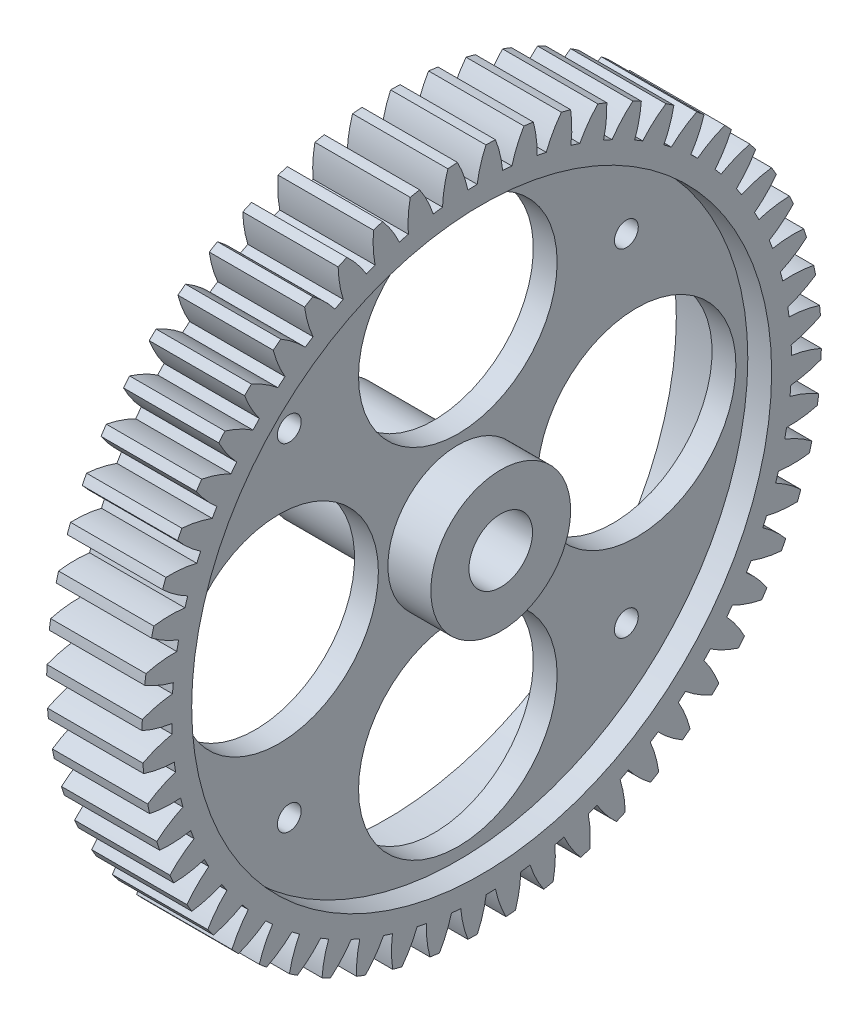
SolidWorks part; units mm, degrees
ref_plane "Front Plane" through (0, 0, 0) normal (0, 0, 1) x (1, 0, 0)
ref_plane "Top Plane" through (0, 0, 0) normal (0, 1, 0) x (1, 0, 0)
ref_plane "Right Plane" through (0, 0, 0) normal (1, 0, 0) x (0, 0, -1)
sketch "Sketch1" plane through (0, 0, 0) normal (1, 0, 0) x (0, 0, -1)
  line L0 (0, 0) -> (0.1063, 3.9986) construction
  line L1 (1.0369, 38.9862) -> (1.1366, 42.7349) construction
  line L2 (22.5, 0) -> (0, 0) construction
  line L3 (0, 0) -> (21.2132, -21.2132) construction
  circle A0 centre (0, 0) radius 42.75 construction
  circle A1 centre (0, 0) radius 41.375 construction
  circle A2 centre (0, 0) radius 39 construction
  circle A3 centre (0, 0) radius 4
  arc A4 (0, 41.375) -> (2.1992, 41.3165) centre (0, 0) cw
  arc A5 (-0.5634, 38.9959) -> (2.6354, 38.9109) centre (0, 0) cw
  arc A6 (0.5367, 42.7466) -> (1.7362, 42.7147) centre (0, 0) cw
  arc A7 (1.7362, 42.7147) -> (2.6354, 38.9109) centre (-11.2723, 37.6315) cw
  arc A8 (0.5367, 42.7466) -> (-0.5634, 38.9959) centre (13.2566, 36.9791) ccw
  arc A9 (5.3194, 42.4178) -> (3.8063, 38.8138) centre (17.3136, 35.2623) ccw
  arc A10 (3.8063, 38.8138) -> (6.9755, 38.3711) centre (0, 0) cw
  arc A11 (6.5078, 42.2518) -> (6.9755, 38.3711) centre (-6.988, 38.6569) cw
  arc A12 (5.3194, 42.4178) -> (6.5078, 42.2518) centre (0, 0) cw
  arc A13 (10.0352, 41.5555) -> (8.1281, 38.1436) centre (21.1529, 33.1021) ccw
  arc A14 (8.1281, 38.1436) -> (11.2278, 37.3488) centre (0, 0) cw
  arc A15 (11.1976, 41.2574) -> (11.2278, 37.3488) centre (-2.6159, 39.1963) cw
  arc A16 (10.0352, 41.5555) -> (11.1976, 41.2574) centre (0, 0) cw
  arc A17 (14.6249, 40.1706) -> (12.3477, 36.9937) centre (24.7261, 30.5256) ccw
  arc A18 (12.3477, 36.9937) -> (15.339, 35.8569) centre (0, 0) cw
  arc A19 (15.7466, 39.7443) -> (15.339, 35.8569) centre (1.7891, 39.2427) cw
  arc A20 (14.6249, 40.1706) -> (15.7466, 39.7443) centre (0, 0) cw
  arc A21 (19.0306, 38.2805) -> (16.412, 35.3786) centre (27.9884, 27.5652) ccw
  arc A22 (16.412, 35.3786) -> (19.2572, 33.914) centre (0, 0) cw
  arc A23 (20.0975, 37.7313) -> (19.2572, 33.914) centre (6.1717, 38.7956) cw
  arc A24 (19.0306, 38.2805) -> (20.0975, 37.7313) centre (0, 0) cw
  arc A25 (23.197, 35.9091) -> (20.27, 33.3186) centre (30.8988, 24.2582) ccw
  arc A26 (20.27, 33.3186) -> (22.9333, 31.5446) centre (0, 0) cw
  arc A27 (24.1957, 35.2439) -> (22.9333, 31.5446) centre (10.4766, 37.8607) cw
  arc A28 (23.197, 35.9091) -> (24.1957, 35.2439) centre (0, 0) cw
  arc A29 (27.0717, 33.0861) -> (23.873, 30.8396) centre (33.4205, 20.6461) ccw
  arc A30 (23.873, 30.8396) -> (26.321, 28.7786) centre (0, 0) cw
  arc A31 (27.9896, 32.3132) -> (26.321, 28.7786) centre (14.6498, 36.4496) cw
  arc A32 (27.0717, 33.0861) -> (27.9896, 32.3132) centre (0, 0) cw
  arc A33 (30.6059, 29.847) -> (27.1759, 27.9727) centre (35.522, 16.7743) ccw
  arc A34 (27.1759, 27.9727) -> (29.3777, 25.6506) centre (0, 0) cw
  arc A35 (31.4316, 28.9762) -> (29.3777, 25.6506) centre (18.6387, 34.5802) cw
  arc A36 (30.6059, 29.847) -> (31.4316, 28.9762) centre (0, 0) cw
  arc A37 (33.7553, 26.2325) -> (30.1369, 24.7541) centre (37.1768, 12.6917) ccw
  arc A38 (30.1369, 24.7541) -> (32.0649, 22.2001) centre (0, 0) cw
  arc A39 (34.4782, 25.2748) -> (32.0649, 22.2001) centre (22.3933, 32.2759) cw
  arc A40 (33.7553, 26.2325) -> (34.4782, 25.2748) centre (0, 0) cw
  arc A41 (36.4801, 22.2882) -> (32.719, 21.2242) centre (38.364, 8.4494) ccw
  arc A42 (32.719, 21.2242) -> (34.3489, 18.4703) centre (0, 0) cw
  arc A43 (37.0913, 21.2555) -> (34.3489, 18.4703) centre (25.8662, 29.5657) cw
  arc A44 (36.4801, 22.2882) -> (37.0913, 21.2555) centre (0, 0) cw
  arc A45 (38.7462, 18.0636) -> (34.8896, 17.4274) centre (39.0688, 4.1008) ccw
  arc A46 (34.8896, 17.4274) -> (36.2009, 14.5084) centre (0, 0) cw
  arc A47 (39.238, 16.9689) -> (36.2009, 14.5084) centre (29.0139, 26.4837) cw
  arc A48 (38.7462, 18.0636) -> (39.238, 16.9689) centre (0, 0) cw
  arc A49 (40.5251, 13.6118) -> (36.6215, 13.4114) centre (39.2823, -0.2993) ccw
  arc A50 (36.6215, 13.4114) -> (37.5977, 10.3639) centre (0, 0) cw
  arc A51 (40.8912, 12.469) -> (37.5977, 10.3639) centre (31.7967, 23.0686) cw
  arc A52 (40.5251, 13.6118) -> (40.8912, 12.469) centre (0, 0) cw
  arc A53 (41.7943, 8.9888) -> (37.8928, 9.2267) centre (39.0018, -4.6956) ccw
  arc A54 (37.8928, 9.2267) -> (38.5217, 6.0891) centre (0, 0) cw
  arc A55 (42.0301, 7.8122) -> (38.5217, 6.0891) centre (34.1796, 19.3635) cw
  arc A56 (41.7943, 8.9888) -> (42.0301, 7.8122) centre (0, 0) cw
  arc A57 (42.5379, 4.2528) -> (38.6876, 4.9261) centre (38.2309, -9.0329) ccw
  arc A58 (38.6876, 4.9261) -> (38.9613, 1.7378) centre (0, 0) cw
  arc A59 (42.6405, 3.0572) -> (38.9613, 1.7378) centre (36.1327, 15.4148) cw
  arc A60 (42.5379, 4.2528) -> (42.6405, 3.0572) centre (0, 0) cw
  arc A61 (42.7466, -0.5367) -> (38.9959, 0.5634) centre (36.9791, -13.2566) ccw
  arc A62 (38.9959, 0.5634) -> (38.9109, -2.6354) centre (0, 0) cw
  arc A63 (42.7147, -1.7362) -> (38.9109, -2.6354) centre (37.6315, 11.2723) cw
  arc A64 (42.7466, -0.5367) -> (42.7147, -1.7362) centre (0, 0) cw
  arc A65 (42.4178, -5.3194) -> (38.8138, -3.8063) centre (35.2623, -17.3136) ccw
  arc A66 (38.8138, -3.8063) -> (38.3711, -6.9755) centre (0, 0) cw
  arc A67 (42.2518, -6.5078) -> (38.3711, -6.9755) centre (38.6569, 6.988) cw
  arc A68 (42.4178, -5.3194) -> (42.2518, -6.5078) centre (0, 0) cw
  arc A69 (41.5555, -10.0352) -> (38.1436, -8.1281) centre (33.1021, -21.1529) ccw
  arc A70 (38.1436, -8.1281) -> (37.3488, -11.2278) centre (0, 0) cw
  arc A71 (41.2574, -11.1976) -> (37.3488, -11.2278) centre (39.1963, 2.6159) cw
  arc A72 (41.5555, -10.0352) -> (41.2574, -11.1976) centre (0, 0) cw
  arc A73 (40.1706, -14.6249) -> (36.9937, -12.3477) centre (30.5256, -24.7261) ccw
  arc A74 (36.9937, -12.3477) -> (35.8569, -15.339) centre (0, 0) cw
  arc A75 (39.7443, -15.7466) -> (35.8569, -15.339) centre (39.2427, -1.7891) cw
  arc A76 (40.1706, -14.6249) -> (39.7443, -15.7466) centre (0, 0) cw
  arc A77 (38.2805, -19.0306) -> (35.3786, -16.412) centre (27.5652, -27.9884) ccw
  arc A78 (35.3786, -16.412) -> (33.914, -19.2572) centre (0, 0) cw
  arc A79 (37.7313, -20.0975) -> (33.914, -19.2572) centre (38.7956, -6.1717) cw
  arc A80 (38.2805, -19.0306) -> (37.7313, -20.0975) centre (0, 0) cw
  arc A81 (35.9091, -23.197) -> (33.3186, -20.27) centre (24.2582, -30.8988) ccw
  arc A82 (33.3186, -20.27) -> (31.5446, -22.9333) centre (0, 0) cw
  arc A83 (35.2439, -24.1957) -> (31.5446, -22.9333) centre (37.8607, -10.4766) cw
  arc A84 (35.9091, -23.197) -> (35.2439, -24.1957) centre (0, 0) cw
  arc A85 (33.0861, -27.0717) -> (30.8396, -23.873) centre (20.6461, -33.4205) ccw
  arc A86 (30.8396, -23.873) -> (28.7786, -26.321) centre (0, 0) cw
  arc A87 (32.3132, -27.9896) -> (28.7786, -26.321) centre (36.4496, -14.6498) cw
  arc A88 (33.0861, -27.0717) -> (32.3132, -27.9896) centre (0, 0) cw
  arc A89 (29.847, -30.6059) -> (27.9727, -27.1759) centre (16.7743, -35.522) ccw
  arc A90 (27.9727, -27.1759) -> (25.6506, -29.3777) centre (0, 0) cw
  arc A91 (28.9762, -31.4316) -> (25.6506, -29.3777) centre (34.5802, -18.6387) cw
  arc A92 (29.847, -30.6059) -> (28.9762, -31.4316) centre (0, 0) cw
  arc A93 (26.2325, -33.7553) -> (24.7541, -30.1369) centre (12.6917, -37.1768) ccw
  arc A94 (24.7541, -30.1369) -> (22.2001, -32.0649) centre (0, 0) cw
  arc A95 (25.2748, -34.4782) -> (22.2001, -32.0649) centre (32.2759, -22.3933) cw
  arc A96 (26.2325, -33.7553) -> (25.2748, -34.4782) centre (0, 0) cw
  arc A97 (22.2882, -36.4801) -> (21.2242, -32.719) centre (8.4494, -38.364) ccw
  arc A98 (21.2242, -32.719) -> (18.4703, -34.3489) centre (0, 0) cw
  arc A99 (21.2555, -37.0913) -> (18.4703, -34.3489) centre (29.5657, -25.8662) cw
  arc A100 (22.2882, -36.4801) -> (21.2555, -37.0913) centre (0, 0) cw
  arc A101 (18.0636, -38.7462) -> (17.4274, -34.8896) centre (4.1008, -39.0688) ccw
  arc A102 (17.4274, -34.8896) -> (14.5084, -36.2009) centre (0, 0) cw
  arc A103 (16.9689, -39.238) -> (14.5084, -36.2009) centre (26.4837, -29.0139) cw
  arc A104 (18.0636, -38.7462) -> (16.9689, -39.238) centre (0, 0) cw
  arc A105 (13.6118, -40.5251) -> (13.4114, -36.6215) centre (-0.2993, -39.2823) ccw
  arc A106 (13.4114, -36.6215) -> (10.3639, -37.5977) centre (0, 0) cw
  arc A107 (12.469, -40.8912) -> (10.3639, -37.5977) centre (23.0686, -31.7967) cw
  arc A108 (13.6118, -40.5251) -> (12.469, -40.8912) centre (0, 0) cw
  arc A109 (8.9888, -41.7943) -> (9.2267, -37.8928) centre (-4.6956, -39.0018) ccw
  arc A110 (9.2267, -37.8928) -> (6.0891, -38.5217) centre (0, 0) cw
  arc A111 (7.8122, -42.0301) -> (6.0891, -38.5217) centre (19.3635, -34.1796) cw
  arc A112 (8.9888, -41.7943) -> (7.8122, -42.0301) centre (0, 0) cw
  arc A113 (4.2528, -42.5379) -> (4.9261, -38.6876) centre (-9.0329, -38.2309) ccw
  arc A114 (4.9261, -38.6876) -> (1.7378, -38.9613) centre (0, 0) cw
  arc A115 (3.0572, -42.6405) -> (1.7378, -38.9613) centre (15.4148, -36.1327) cw
  arc A116 (4.2528, -42.5379) -> (3.0572, -42.6405) centre (0, 0) cw
  arc A117 (-0.5367, -42.7466) -> (0.5634, -38.9959) centre (-13.2566, -36.9791) ccw
  arc A118 (0.5634, -38.9959) -> (-2.6354, -38.9109) centre (0, 0) cw
  arc A119 (-1.7362, -42.7147) -> (-2.6354, -38.9109) centre (11.2723, -37.6315) cw
  arc A120 (-0.5367, -42.7466) -> (-1.7362, -42.7147) centre (0, 0) cw
  arc A121 (-5.3194, -42.4178) -> (-3.8063, -38.8138) centre (-17.3136, -35.2623) ccw
  arc A122 (-3.8063, -38.8138) -> (-6.9755, -38.3711) centre (0, 0) cw
  arc A123 (-6.5078, -42.2518) -> (-6.9755, -38.3711) centre (6.988, -38.6569) cw
  arc A124 (-5.3194, -42.4178) -> (-6.5078, -42.2518) centre (0, 0) cw
  arc A125 (-10.0352, -41.5555) -> (-8.1281, -38.1436) centre (-21.1529, -33.1021) ccw
  arc A126 (-8.1281, -38.1436) -> (-11.2278, -37.3488) centre (0, 0) cw
  arc A127 (-11.1976, -41.2574) -> (-11.2278, -37.3488) centre (2.6159, -39.1963) cw
  arc A128 (-10.0352, -41.5555) -> (-11.1976, -41.2574) centre (0, 0) cw
  arc A129 (-14.6249, -40.1706) -> (-12.3477, -36.9937) centre (-24.7261, -30.5256) ccw
  arc A130 (-12.3477, -36.9937) -> (-15.339, -35.8569) centre (0, 0) cw
  arc A131 (-15.7466, -39.7443) -> (-15.339, -35.8569) centre (-1.7891, -39.2427) cw
  arc A132 (-14.6249, -40.1706) -> (-15.7466, -39.7443) centre (0, 0) cw
  arc A133 (-19.0306, -38.2805) -> (-16.412, -35.3786) centre (-27.9884, -27.5652) ccw
  arc A134 (-16.412, -35.3786) -> (-19.2572, -33.914) centre (0, 0) cw
  arc A135 (-20.0975, -37.7313) -> (-19.2572, -33.914) centre (-6.1717, -38.7956) cw
  arc A136 (-19.0306, -38.2805) -> (-20.0975, -37.7313) centre (0, 0) cw
  arc A137 (-23.197, -35.9091) -> (-20.27, -33.3186) centre (-30.8988, -24.2582) ccw
  arc A138 (-20.27, -33.3186) -> (-22.9333, -31.5446) centre (0, 0) cw
  arc A139 (-24.1957, -35.2439) -> (-22.9333, -31.5446) centre (-10.4766, -37.8607) cw
  arc A140 (-23.197, -35.9091) -> (-24.1957, -35.2439) centre (0, 0) cw
  arc A141 (-27.0717, -33.0861) -> (-23.873, -30.8396) centre (-33.4205, -20.6461) ccw
  arc A142 (-23.873, -30.8396) -> (-26.321, -28.7786) centre (0, 0) cw
  arc A143 (-27.9896, -32.3132) -> (-26.321, -28.7786) centre (-14.6498, -36.4496) cw
  arc A144 (-27.0717, -33.0861) -> (-27.9896, -32.3132) centre (0, 0) cw
  arc A145 (-30.6059, -29.847) -> (-27.1759, -27.9727) centre (-35.522, -16.7743) ccw
  arc A146 (-27.1759, -27.9727) -> (-29.3777, -25.6506) centre (0, 0) cw
  arc A147 (-31.4316, -28.9762) -> (-29.3777, -25.6506) centre (-18.6387, -34.5802) cw
  arc A148 (-30.6059, -29.847) -> (-31.4316, -28.9762) centre (0, 0) cw
  arc A149 (-33.7553, -26.2325) -> (-30.1369, -24.7541) centre (-37.1768, -12.6917) ccw
  arc A150 (-30.1369, -24.7541) -> (-32.0649, -22.2001) centre (0, 0) cw
  arc A151 (-34.4782, -25.2748) -> (-32.0649, -22.2001) centre (-22.3933, -32.2759) cw
  arc A152 (-33.7553, -26.2325) -> (-34.4782, -25.2748) centre (0, 0) cw
  arc A153 (-36.4801, -22.2882) -> (-32.719, -21.2242) centre (-38.364, -8.4494) ccw
  arc A154 (-32.719, -21.2242) -> (-34.3489, -18.4703) centre (0, 0) cw
  arc A155 (-37.0913, -21.2555) -> (-34.3489, -18.4703) centre (-25.8662, -29.5657) cw
  arc A156 (-36.4801, -22.2882) -> (-37.0913, -21.2555) centre (0, 0) cw
  arc A157 (-38.7462, -18.0636) -> (-34.8896, -17.4274) centre (-39.0688, -4.1008) ccw
  arc A158 (-34.8896, -17.4274) -> (-36.2009, -14.5084) centre (0, 0) cw
  arc A159 (-39.238, -16.9689) -> (-36.2009, -14.5084) centre (-29.0139, -26.4837) cw
  arc A160 (-38.7462, -18.0636) -> (-39.238, -16.9689) centre (0, 0) cw
  arc A161 (-40.5251, -13.6118) -> (-36.6215, -13.4114) centre (-39.2823, 0.2993) ccw
  arc A162 (-36.6215, -13.4114) -> (-37.5977, -10.3639) centre (0, 0) cw
  arc A163 (-40.8912, -12.469) -> (-37.5977, -10.3639) centre (-31.7967, -23.0686) cw
  arc A164 (-40.5251, -13.6118) -> (-40.8912, -12.469) centre (0, 0) cw
  arc A165 (-41.7943, -8.9888) -> (-37.8928, -9.2267) centre (-39.0018, 4.6956) ccw
  arc A166 (-37.8928, -9.2267) -> (-38.5217, -6.0891) centre (0, 0) cw
  arc A167 (-42.0301, -7.8122) -> (-38.5217, -6.0891) centre (-34.1796, -19.3635) cw
  arc A168 (-41.7943, -8.9888) -> (-42.0301, -7.8122) centre (0, 0) cw
  arc A169 (-42.5379, -4.2528) -> (-38.6876, -4.9261) centre (-38.2309, 9.0329) ccw
  arc A170 (-38.6876, -4.9261) -> (-38.9613, -1.7378) centre (0, 0) cw
  arc A171 (-42.6405, -3.0572) -> (-38.9613, -1.7378) centre (-36.1327, -15.4148) cw
  arc A172 (-42.5379, -4.2528) -> (-42.6405, -3.0572) centre (0, 0) cw
  arc A173 (-42.7466, 0.5367) -> (-38.9959, -0.5634) centre (-36.9791, 13.2566) ccw
  arc A174 (-38.9959, -0.5634) -> (-38.9109, 2.6354) centre (0, 0) cw
  arc A175 (-42.7147, 1.7362) -> (-38.9109, 2.6354) centre (-37.6315, -11.2723) cw
  arc A176 (-42.7466, 0.5367) -> (-42.7147, 1.7362) centre (0, 0) cw
  arc A177 (-42.4178, 5.3194) -> (-38.8138, 3.8063) centre (-35.2623, 17.3136) ccw
  arc A178 (-38.8138, 3.8063) -> (-38.3711, 6.9755) centre (0, 0) cw
  arc A179 (-42.2518, 6.5078) -> (-38.3711, 6.9755) centre (-38.6569, -6.988) cw
  arc A180 (-42.4178, 5.3194) -> (-42.2518, 6.5078) centre (0, 0) cw
  arc A181 (-41.5555, 10.0352) -> (-38.1436, 8.1281) centre (-33.1021, 21.1529) ccw
  arc A182 (-38.1436, 8.1281) -> (-37.3488, 11.2278) centre (0, 0) cw
  arc A183 (-41.2574, 11.1976) -> (-37.3488, 11.2278) centre (-39.1963, -2.6159) cw
  arc A184 (-41.5555, 10.0352) -> (-41.2574, 11.1976) centre (0, 0) cw
  arc A185 (-40.1706, 14.6249) -> (-36.9937, 12.3477) centre (-30.5256, 24.7261) ccw
  arc A186 (-36.9937, 12.3477) -> (-35.8569, 15.339) centre (0, 0) cw
  arc A187 (-39.7443, 15.7466) -> (-35.8569, 15.339) centre (-39.2427, 1.7891) cw
  arc A188 (-40.1706, 14.6249) -> (-39.7443, 15.7466) centre (0, 0) cw
  arc A189 (-38.2805, 19.0306) -> (-35.3786, 16.412) centre (-27.5652, 27.9884) ccw
  arc A190 (-35.3786, 16.412) -> (-33.914, 19.2572) centre (0, 0) cw
  arc A191 (-37.7313, 20.0975) -> (-33.914, 19.2572) centre (-38.7956, 6.1717) cw
  arc A192 (-38.2805, 19.0306) -> (-37.7313, 20.0975) centre (0, 0) cw
  arc A193 (-35.9091, 23.197) -> (-33.3186, 20.27) centre (-24.2582, 30.8988) ccw
  arc A194 (-33.3186, 20.27) -> (-31.5446, 22.9333) centre (0, 0) cw
  arc A195 (-35.2439, 24.1957) -> (-31.5446, 22.9333) centre (-37.8607, 10.4766) cw
  arc A196 (-35.9091, 23.197) -> (-35.2439, 24.1957) centre (0, 0) cw
  arc A197 (-33.0861, 27.0717) -> (-30.8396, 23.873) centre (-20.6461, 33.4205) ccw
  arc A198 (-30.8396, 23.873) -> (-28.7786, 26.321) centre (0, 0) cw
  arc A199 (-32.3132, 27.9896) -> (-28.7786, 26.321) centre (-36.4496, 14.6498) cw
  arc A200 (-33.0861, 27.0717) -> (-32.3132, 27.9896) centre (0, 0) cw
  arc A201 (-29.847, 30.6059) -> (-27.9727, 27.1759) centre (-16.7743, 35.522) ccw
  arc A202 (-27.9727, 27.1759) -> (-25.6506, 29.3777) centre (0, 0) cw
  arc A203 (-28.9762, 31.4316) -> (-25.6506, 29.3777) centre (-34.5802, 18.6387) cw
  arc A204 (-29.847, 30.6059) -> (-28.9762, 31.4316) centre (0, 0) cw
  arc A205 (-26.2325, 33.7553) -> (-24.7541, 30.1369) centre (-12.6917, 37.1768) ccw
  arc A206 (-24.7541, 30.1369) -> (-22.2001, 32.0649) centre (0, 0) cw
  arc A207 (-25.2748, 34.4782) -> (-22.2001, 32.0649) centre (-32.2759, 22.3933) cw
  arc A208 (-26.2325, 33.7553) -> (-25.2748, 34.4782) centre (0, 0) cw
  arc A209 (-22.2882, 36.4801) -> (-21.2242, 32.719) centre (-8.4494, 38.364) ccw
  arc A210 (-21.2242, 32.719) -> (-18.4703, 34.3489) centre (0, 0) cw
  arc A211 (-21.2555, 37.0913) -> (-18.4703, 34.3489) centre (-29.5657, 25.8662) cw
  arc A212 (-22.2882, 36.4801) -> (-21.2555, 37.0913) centre (0, 0) cw
  arc A213 (-18.0636, 38.7462) -> (-17.4274, 34.8896) centre (-4.1008, 39.0688) ccw
  arc A214 (-17.4274, 34.8896) -> (-14.5084, 36.2009) centre (0, 0) cw
  arc A215 (-16.9689, 39.238) -> (-14.5084, 36.2009) centre (-26.4837, 29.0139) cw
  arc A216 (-18.0636, 38.7462) -> (-16.9689, 39.238) centre (0, 0) cw
  arc A217 (-13.6118, 40.5251) -> (-13.4114, 36.6215) centre (0.2993, 39.2823) ccw
  arc A218 (-13.4114, 36.6215) -> (-10.3639, 37.5977) centre (0, 0) cw
  arc A219 (-12.469, 40.8912) -> (-10.3639, 37.5977) centre (-23.0686, 31.7967) cw
  arc A220 (-13.6118, 40.5251) -> (-12.469, 40.8912) centre (0, 0) cw
  arc A221 (-8.9888, 41.7943) -> (-9.2267, 37.8928) centre (4.6956, 39.0018) ccw
  arc A222 (-9.2267, 37.8928) -> (-6.0891, 38.5217) centre (0, 0) cw
  arc A223 (-7.8122, 42.0301) -> (-6.0891, 38.5217) centre (-19.3635, 34.1796) cw
  arc A224 (-8.9888, 41.7943) -> (-7.8122, 42.0301) centre (0, 0) cw
  arc A225 (-4.2528, 42.5379) -> (-4.9261, 38.6876) centre (9.0329, 38.2309) ccw
  arc A226 (-4.9261, 38.6876) -> (-1.7378, 38.9613) centre (0, 0) cw
  arc A227 (-3.0572, 42.6405) -> (-1.7378, 38.9613) centre (-15.4148, 36.1327) cw
  arc A228 (-4.2528, 42.5379) -> (-3.0572, 42.6405) centre (0, 0) cw
  circle A229 centre (0, 0) radius 39
  circle A230 centre (0, 0) radius 22.5 construction
  circle A231 centre (0, 22.5) radius 12.5
  circle A234 centre (22.5, 0) radius 12.5
  circle A235 centre (0, -22.5) radius 12.5
  circle A236 centre (-22.5, 0) radius 12.5
  circle A237 centre (0, 0) radius 30 construction
  circle A238 centre (21.2132, -21.2132) radius 1.5
  circle A239 centre (-21.2132, -21.2132) radius 1.5
  circle A240 centre (-21.2132, 21.2132) radius 1.5
  circle A241 centre (21.2132, 21.2132) radius 1.5
  point P13 (1.0369, 38.9862)
  point P16 (1.1366, 42.7349)
  point P351 (0, 0)
  point P360 (0, 0)
  point P364 (0, 0)
  point P374 (0, 0)
  dimension "D1" = 85.5
  dimension "D2" = 82.75
  dimension "D3" = 78
  dimension "D4" = 8
  dimension "D5" = 2.2
  dimension "D9" = 45
  dimension "D10" = 4
  dimension "D6" = 3.2
  dimension "D7" = 1.2
  dimension "D8" = 56
extrude "Boss-Extrude1" add sketch "Sketch1" along normal blind 12 contours A62 A229 A58 A54 A50 A46 A42 A38 A34 A30 A26 A22 A18 A14 A10 A5 A226 A222 A218 A214 A210 A206 A202 A198 A194 A190 A186 | A144 A141 A142 A143 | A140 A137 A138 A139 | A136 A133 A134 A135 | A132 A129 A130 A131 | A128 A125 A126 A127 | A124 A121 A122 A123 | A120 A117 A118 A119 | A116 A113 A114 A115 | A112 A109 A110 A111 | A108 A105 A106 A107 | A104 A101 A102 A103 | A100 A97 A98 A99 | A96 A93 A94 A95 | A92 A89 A90 A91 | A88 A85 A86 A87 | A84 A81 A82 A83 | A148 A145 A146 A147 | A152 A149 A150 A151 | A156 A153 A154 A155 | A160 A157 A158 A159 | A164 A161 A162 A163 | A168 A165 A166 A167 | A172 A169 A170 A171 | A176 A173 A174 A175 | A180 A177 A178 A179 | A184 A181 A182 A183 | A60 A57 A58 A59 | A64 A61 A62 A63 | A68 A65 A66 A67 | A72 A69 A70 A71 | A76 A73 A74 A75 | A80 A77 A78 A79 | A188 A185 A186 A187 | A192 A189 A190 A191 | A196 A193 A194 A195 | A200 A197 A198 A199 | A204 A201 A202 A203 | A208 A205 A206 A207 | A212 A209 A210 A211 | A216 A213 A214 A215 | A220 A217 A218 A219 | A224 A221 A222 A223 | A228 A225 A226 A227 | A12 A9 A10 A11 | A16 A13 A14 A15 | A20 A17 A18 A19 | A56 A53 A54 A55 | A52 A49 A50 A51 | A48 A45 A46 A47 | A44 A41 A42 A43 | A40 A37 A38 A39 | A36 A33 A34 A35 | A32 A29 A30 A31 | A28 A25 A26 A27 | A24 A21 A22 A23 | A6 A8 A4 A7 | A4 A8 A5 A7
sketch "Sketch4" plane through (12, 0, 0) normal (1, 0, 0) x (0, 0, -1)
  circle A0 centre (0, 0) radius 36.5
extrude "Cut-Extrude1" cut sketch "Sketch4" against normal blind 3
sketch "Sketch5" plane through (0, 0, 0) normal (-1, 0, 0) x (0, 0, 1)
  circle A0 centre (0, 0) radius 36.5
extrude "Cut-Extrude2" cut sketch "Sketch5" against normal blind 6
sketch "Sketch6" plane through (9, 0, 0) normal (1, 0, 0) x (0, 0, -1)
  circle A0 centre (0, 0) radius 8.8
  circle A1 centre (0, 0) radius 4
  dimension "D1" = 17.6
extrude "Boss-Extrude2" add sketch "Sketch6" along normal blind 5.4
sketch "Sketch7" plane through (6, 0, 0) normal (-1, 0, 0) x (0, 0, 1)
  circle A0 centre (0, 0) radius 4
  circle A1 centre (0, 0) radius 7.2
extrude "Boss-Extrude3" add sketch "Sketch7" along normal blind 13.5
